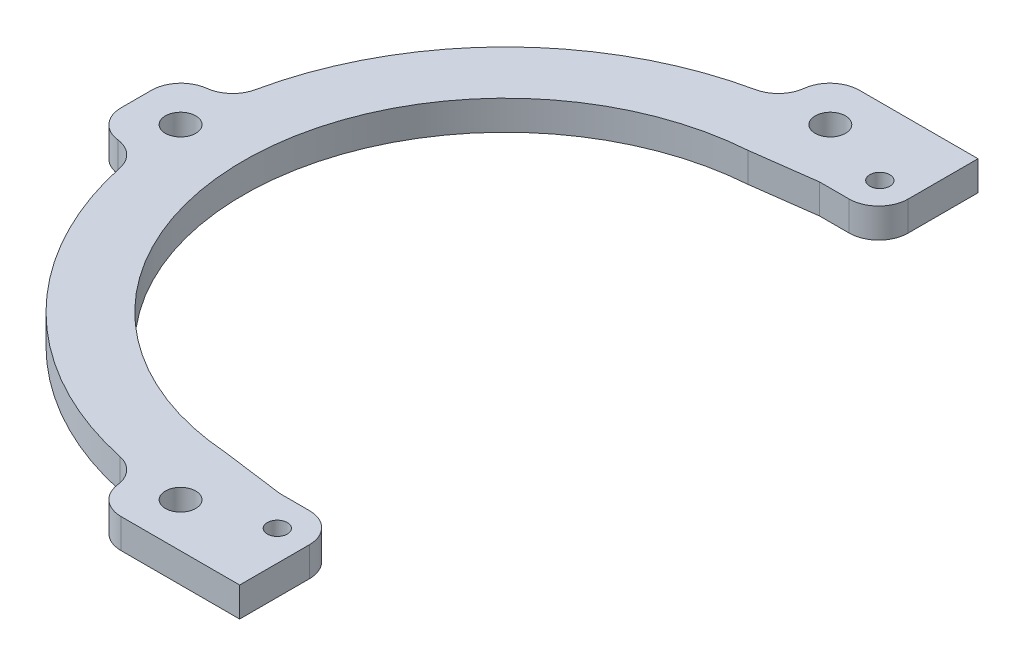
SolidWorks part; units mm, degrees
other "Markup1"
sketch "Sketch15" plane through (-79.375, 6.35, -79.375) normal (0, 1, 0) x (1, 0, 0)
other "Markup2"
sketch "Sketch16" plane through (-79.375, 6.35, -79.375) normal (0, 1, 0) x (1, 0, 0)
material "6061-T6 (SS)"
ref_plane "Front Plane" through (0, 0, 0) normal (0, 0, 1) x (1, 0, 0)
ref_plane "Top Plane" through (0, 0, 0) normal (0, 1, 0) x (1, 0, 0)
ref_plane "Right Plane" through (0, 0, 0) normal (1, 0, 0) x (0, 0, -1)
sketch "Sketch1" plane through (0, 0, 0) normal (0, 1, 0) x (1, 0, 0)
  circle A0 centre (0, 0) radius 56.3562
  circle A1 centre (0, 0) radius 69.85
  dimension "D1" = 112.7125
  dimension "D2" = 139.7
extrude "Boss-Extrude1" add sketch "Sketch1" along normal blind 6.35
sketch "Sketch5" plane through (0, 6.35, 0) normal (0, 1, 0) x (1, 0, 0)
  line L0 (0, 0) -> (0, 63.5) construction
  line L1 (-9.525, 63.5) -> (9.525, 63.5)
  line L2 (-9.525, 63.5) -> (-9.525, 79.375)
  line L5 (-9.525, 79.375) -> (9.525, 79.375)
  line L6 (9.525, 79.375) -> (9.525, 63.5)
  dimension "D1" = 63.5
  dimension "D2" = 19.05
  dimension "D3" = 15.875
extrude "Boss-Extrude2" add sketch "Sketch5" against normal blind 6.35
fillet "Fillet1" radius 6.35 2 edges at (-9.525, 3.175, -69.1975) (9.525, 3.175, -69.1975)
pattern_circular "CirPattern2" count 3 every 90 about axis through (0, 0, 0) along (0, 1, 0) of "Boss-Extrude2", "Fillet1"
sketch "Sketch11" plane through (0, 0, 0) normal (0, -1, 0) x (1, 0, 0)
  circle A0 centre (0, -69.85) radius 3.2639
  dimension "D1" = 6.5278
  dimension "D2" = 69.85
extrude "Cut-Extrude2" cut sketch "Sketch11" against normal through all
pattern_circular "CirPattern3" count 3 every 90 about axis through (0, 0, 0) along (0, 1, 0) of "Cut-Extrude2"
sketch "Sketch14" plane through (0, 6.35, 0) normal (0, 1, 0) x (1, 0, 0)
  line L5 (-10.795, 58.018) -> (-10.795, 55.3127) construction
  line L10 (9.525, 58.018) -> (-10.795, 58.018) construction
  line L14 (-56.3562, 0) -> (116.4885, 0) construction
  line L16 (76.1412, 74.528) -> (76.1412, -74.528)
  line L22 (9.525, 74.528) -> (9.525, 58.018)
  line L23 (9.525, 74.528) -> (76.1412, 74.528)
  line L24 (-10.795, 55.3127) -> (9.525, 58.018)
  line L25 (-10.795, 55.3127) -> (-10.795, -55.3127)
  line L26 (9.525, -58.018) -> (-10.795, -58.018) construction
  line L27 (-10.795, -58.018) -> (-10.795, -55.3127) construction
  line L28 (-10.795, -55.3127) -> (9.525, -58.018)
  line L29 (9.525, -74.528) -> (76.1412, -74.528)
  line L30 (9.525, -74.528) -> (9.525, -58.018)
  circle A1 centre (0, 0) radius 56.3562 construction
  point P9 (-10.795, 0)
  point P10 (76.1412, 0)
  point P11 (-10.795, 0)
  point P17 (76.1412, 0)
  dimension "D1" = 90
  dimension "D2" = 20.32
  dimension "D3" = 90
  dimension "D4" = 16.51
extrude "Cut-Extrude4" cut sketch "Sketch14" against normal through all
fillet "Fillet8" radius 6.35 4 edges at (-9.525, 3.175, 79.375) (-79.375, 3.175, 9.525) (-79.375, 3.175, -9.525) (-9.525, 3.175, -79.375)
sketch "Sketch22" plane through (9.525, 0, 0) normal (1, 0, 0) x (0, 0, -1)
  line L1 (58.018, 6.35) -> (79.375, 6.35)
  line L2 (58.018, 6.35) -> (58.018, 0)
  line L3 (58.018, 0) -> (79.375, 0)
  line L4 (79.375, 6.35) -> (79.375, 0)
  point P6 (0, 0)
  point P7 (61.828, 6.35)
extrude "Boss-Extrude3" add sketch "Sketch22" along normal blind 12.7 contours L2 L1 L4 L3
sketch "Sketch23" plane through (0, 6.35, 0) normal (0, 1, 0) x (1, 0, 0)
  circle A0 centre (15.7226, 64.77) radius 2.1527
  point P0 (0, 0)
  point P2 (16.8406, 70.6015)
  dimension "D1" = 4.3053
  dimension "D2" = 15.7226
  dimension "D3" = 64.77
extrude "Cut-Extrude5" cut sketch "Sketch23" against normal through all
mirror "Mirror1" about plane through (0, 0, 0) normal (0, 0, 1) of "Cut-Extrude5", "Boss-Extrude3"
fillet "Fillet11" radius 6.35 2 edges at (22.225, 3.175, 58.018) (22.225, 3.175, -58.018)
